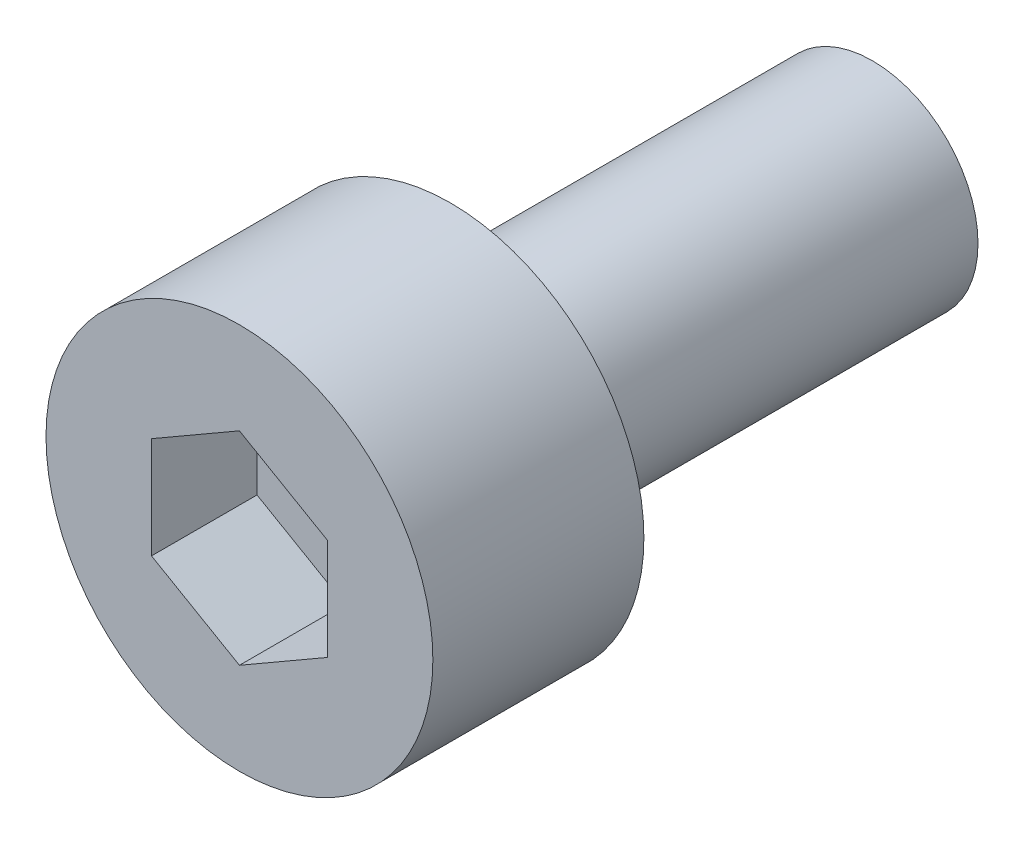
SolidWorks part; units mm, degrees
material "灰铸铁"
ref_plane "前视基准面" through (0, 0, 0) normal (0, 0, 1) x (1, 0, 0)
ref_plane "上视基准面" through (0, 0, 0) normal (0, 1, 0) x (1, 0, 0)
ref_plane "右视基准面" through (0, 0, 0) normal (1, 0, 0) x (0, 0, -1)
sketch "草图1" plane through (0, 0, 0) normal (0, 0, 1) x (1, 0, 0)
  circle A0 centre (0, 0) radius 2.75
  dimension "D1" = 5.5
extrude "凸台-拉伸1" add sketch "草图1" along normal blind 3
sketch "草图2" plane through (0, 0, 3) normal (0, 0, 1) x (1, 0, 0)
  line L1 (0, -1.4434) -> (1.25, -0.7217)
  line L2 (1.25, -0.7217) -> (1.25, 0.7217)
  line L3 (1.25, 0.7217) -> (0, 1.4434)
  line L4 (0, 1.4434) -> (-1.25, 0.7217)
  line L5 (-1.25, 0.7217) -> (-1.25, -0.7217)
  line L6 (-1.25, -0.7217) -> (0, -1.4434)
  circle A0 centre (0, 0) radius 1.25 construction
  dimension "D1" = 2.5
extrude "切除-拉伸1" cut sketch "草图2" against normal blind 1.5
sketch "草图3" plane through (0, 0, 0) normal (0, 0, -1) x (-1, 0, 0)
  circle A0 centre (0, 0) radius 1.5
extrude "凸台-拉伸2" add sketch "草图3" along normal blind 6
